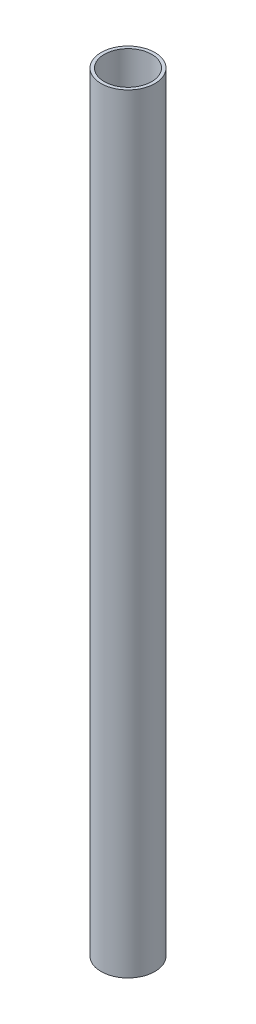
SolidWorks part; units mm, degrees
ref_plane "Front Plane" through (0, 0, 0) normal (0, 0, 1) x (1, 0, 0)
ref_plane "Top Plane" through (0, 0, 0) normal (0, 1, 0) x (1, 0, 0)
ref_plane "Right Plane" through (0, 0, 0) normal (1, 0, 0) x (0, 0, -1)
sketch "Sketch1" plane through (0, 0, 0) normal (0, 1, 0) x (1, 0, 0)
  circle A0 centre (0, 0) radius 10.5
  circle A1 centre (0, 0) radius 9.25
  dimension "D1" = 21
  dimension "D2" = 18.5
extrude "Boss-Extrude1" add sketch "Sketch1" along normal blind 300
